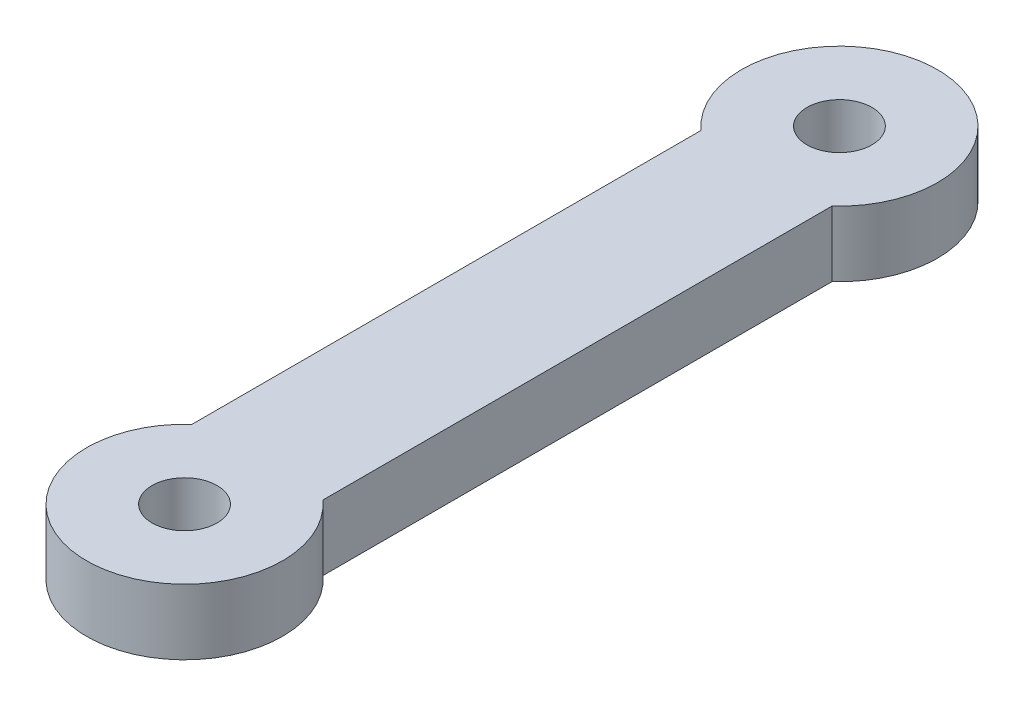
SolidWorks part; units mm, degrees
ref_plane "Top Plane" through (0, 0, 0) normal (0, 0, 1) x (1, 0, 0)
ref_plane "Front Plane" through (0, 0, 0) normal (0, 1, 0) x (1, 0, 0)
ref_plane "Right Plane" through (0, 0, 0) normal (1, 0, 0) x (0, 0, -1)
sketch "Profile Sketch" plane through (0, 0, 0) normal (0, 1, 0) x (1, 0, 0)
  line L0 (-3.175, -3.533) -> (-3.175, -28.217)
  line L1 (0, 0) -> (0, -31.75) construction
  line L2 (3.175, -3.533) -> (3.175, -28.217)
  circle A0 centre (0, 0) radius 1.575
  circle A1 centre (0, 0) radius 4.75
  circle A2 centre (0, -31.75) radius 4.75
  circle A3 centre (0, -31.75) radius 1.575
  dimension "D1" = 3.15
  dimension "D2" = 3.15
  dimension "D3" = 31.75
  dimension "D5" = 3.175
  dimension "D4" = 3.175
extrude "Boss-Extrude1" add sketch "Profile Sketch" along normal blind 3.175
equation "\"D2@Profile Sketch\"=\"D1@Profile Sketch\""
